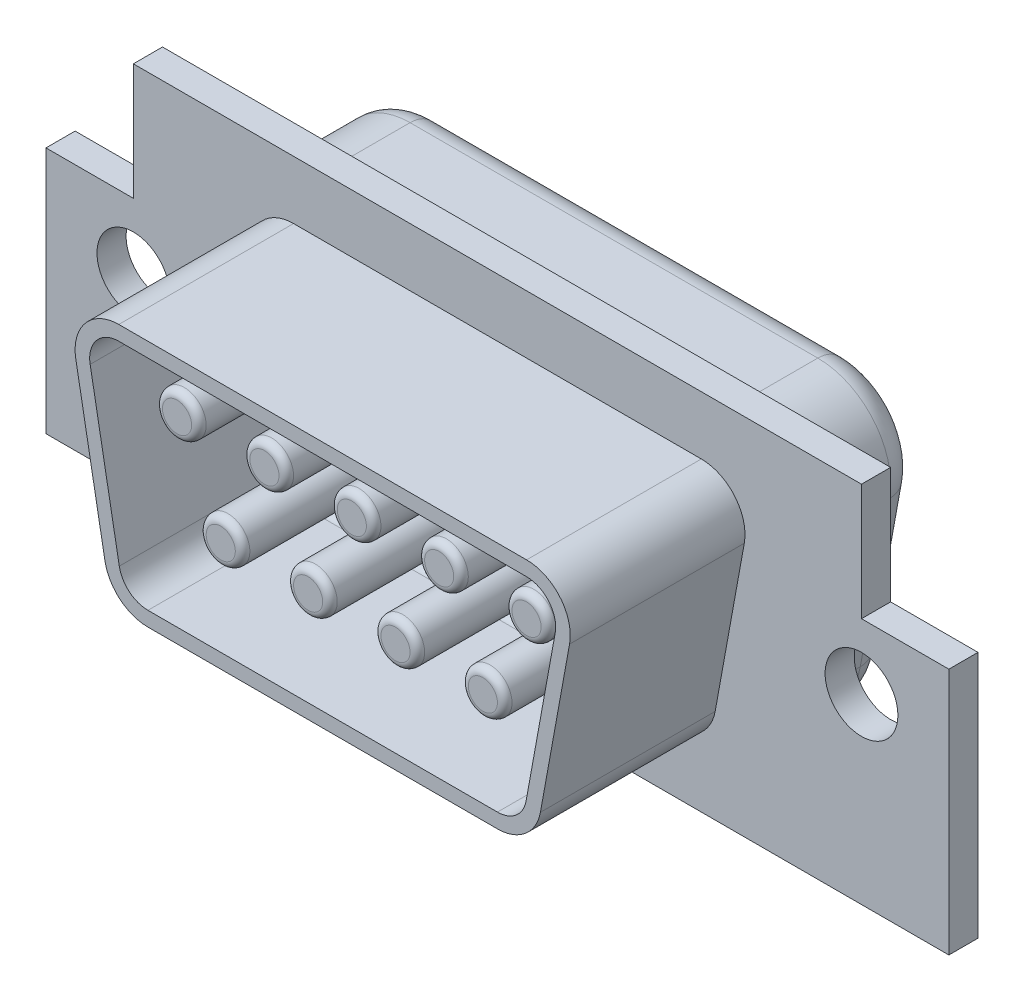
SolidWorks part; units mm, degrees
material "1060 Alloy"
ref_plane "Front Plane" through (0, 0, 0) normal (0, 0, 1) x (1, 0, 0)
ref_plane "Top Plane" through (0, 0, 0) normal (0, 1, 0) x (1, 0, 0)
ref_plane "Right Plane" through (0, 0, 0) normal (1, 0, 0) x (0, 0, -1)
sketch "Sketch1" plane through (0, 0, 0) normal (0, 0, 1) x (1, 0, 0)
  line L0 (-15.5, 6.25) -> (15.5, -6.25) construction
  line L1 (-15.5, 6.25) -> (15.5, 6.25)
  line L2 (-15.5, 6.25) -> (-15.5, -6.25)
  line L3 (-15.5, -6.25) -> (15.5, -6.25)
  line L4 (15.5, 6.25) -> (15.5, -6.25)
  point P4 (0, 0)
  dimension "D1" = 31
  dimension "D2" = 12.5
extrude "Extrude1" add sketch "Sketch1" along normal blind 1
sketch "Sketch2" plane through (0, 0, 1) normal (0, 0, 1) x (1, 0, 0)
  line L5 (7.6692, -4.75) -> (13.0097, -4.8041) construction
  line L6 (-7, 3.75) -> (7, 3.75)
  line L7 (-6, -4.25) -> (6, -4.25)
  line L8 (8.4758, 2.4817) -> (7.4758, -3.0183)
  line L9 (-7, 4.25) -> (7, 4.25)
  line L10 (-8.4758, 2.4817) -> (-7.4758, -3.0183)
  line L11 (7.9839, 2.5711) -> (6.9839, -2.9289)
  line L12 (-6, -3.75) -> (6, -3.75)
  line L13 (-7.9839, 2.5711) -> (-6.9839, -2.9289)
  arc A4 (7.4758, -3.0183) -> (6, -4.25) centre (6, -2.75) cw
  arc A5 (8.4758, 2.4817) -> (7, 4.25) centre (7, 2.75) ccw
  arc A6 (-7, 4.25) -> (-8.4758, 2.4817) centre (-7, 2.75) ccw
  arc A7 (-6, -4.25) -> (-7.4758, -3.0183) centre (-6, -2.75) cw
  arc A8 (7.9839, 2.5711) -> (7, 3.75) centre (7, 2.75) ccw
  arc A9 (6.9839, -2.9289) -> (6, -3.75) centre (6, -2.75) cw
  arc A10 (-6, -3.75) -> (-6.9839, -2.9289) centre (-6, -2.75) cw
  arc A11 (-7, 3.75) -> (-7.9839, 2.5711) centre (-7, 2.75) ccw
  dimension "D8" = 0.5
extrude "Extrude2" add sketch "Sketch2" along normal blind 6
hole_wizard "M3x0.5 Tapped Hole1" positions "3DSketch1" profile "Sketch4" tap size "M3x0.5" standard "Ansi Metric"
sketch3d "3DSketch1"
  line L0 (-15.5, 6.25, 1) -> (-15.5, -6.25, 1) construction
  point P0 (-12.5, 0, 1)
  point P2 (12.5, 0, 1)
  point P7 (-15.5, 0, 1)
  dimension "D1" = 25
  dimension "D2" = 3
sketch "Sketch4" plane through (-12.5, 0, 1) normal (1, 0, 0) x (0, -1, 0)
  line L0 (0, 0) -> (0, 18.2511)
  line L1 (0, 18.2511) -> (1.25, 17.5)
  line L2 (1.25, 17.5) -> (1.25, 0)
  line L5 (1.25, 0) -> (0, 0)
  line L10 (0, 18.2511) -> (-1.25, 17.5) construction
  line L11 (0, -6.35) -> (0, 107.95) construction
  dimension "Tap Drill Dia." = 2.5
  dimension "Tap Drill Depth" = 17.5
  dimension "Drill Angle" = 118
cosmetic thread "Hole Thread1" parameters "D1"=1, "D2"=3
cosmetic thread "Hole Thread2" parameters "D1"=1, "D2"=3
sketch "Sketch6" plane through (0, 0, 0) normal (0, 0, -1) x (-1, 0, 0)
  line L12 (8.4597, -3.1972) -> (9.4597, 2.3028)
  line L13 (-6, -5.25) -> (6, -5.25)
  line L14 (-9.4597, 2.3028) -> (-8.4597, -3.1972)
  line L15 (7, 5.25) -> (-7, 5.25)
  arc A12 (9.4597, 2.3028) -> (7, 5.25) centre (7, 2.75) ccw
  arc A13 (6, -5.25) -> (8.4597, -3.1972) centre (6, -2.75) ccw
  arc A14 (-8.4597, -3.1972) -> (-6, -5.25) centre (-6, -2.75) ccw
  arc A15 (-7, 5.25) -> (-9.4597, 2.3028) centre (-7, 2.75) ccw
extrude "Extrude3" add sketch "Sketch6" along normal blind 4
fillet "Fillet2" radius 1 8 edges at (-8.9597, -0.4472, -4) (-7.6019, -4.6694, -4) (0, -5.25, -4) (7.6019, -4.6694, -4) (8.9597, -0.4472, -4) (8.9194, 4.3519, -4) (0, 5.25, -4) (-8.9194, 4.3519, -4)
sketch "Sketch7" plane through (0, 0, -4) normal (0, 0, -1) x (-1, 0, 0)
  line L12 (6.9839, -2.9289) -> (7.9839, 2.5711)
  line L13 (-6, -3.75) -> (6, -3.75)
  line L14 (-7.9839, 2.5711) -> (-6.9839, -2.9289)
  line L15 (7, 3.75) -> (-7, 3.75)
  arc A12 (7.9839, 2.5711) -> (7, 3.75) centre (7, 2.75) ccw
  arc A13 (6, -3.75) -> (6.9839, -2.9289) centre (6, -2.75) ccw
  arc A14 (-6.9839, -2.9289) -> (-6, -3.75) centre (-6, -2.75) ccw
  arc A15 (-7, 3.75) -> (-7.9839, 2.5711) centre (-7, 2.75) ccw
extrude "Extrude4" add sketch "Sketch7" along normal blind 0.5
sketch "Sketch8" plane through (0, 0, 1) normal (0, 0, 1) x (1, 0, 0)
  line L1 (1.5, -1.5) -> (-1.5, -1.5) construction
  circle A0 centre (-6, 1.5) radius 0.75
  circle A1 centre (-4.5, -1.5) radius 0.75
  circle A2 centre (-3, 1.5) radius 0.75
  circle A3 centre (1.5, -1.5) radius 0.75
  circle A4 centre (0, 1.5) radius 0.75
  circle A5 centre (-1.5, -1.5) radius 0.75
  circle A6 centre (3, 1.5) radius 0.75
  circle A7 centre (4.5, -1.5) radius 0.75
  circle A8 centre (6, 1.5) radius 0.75
  point P19 (0, -1.5)
  dimension "D1" = 1.5
  dimension "D4" = 1.5
  dimension "D5" = 1.5
  dimension "D6" = 1.5
  dimension "D7" = 1.5
  dimension "D8" = 1.5
  dimension "D9" = 1.5
  dimension "D10" = 1.5
  dimension "D11" = 1.5
  dimension "D2" = 3
  dimension "D3" = 1.5
  dimension "D12" = 3
  dimension "D13" = 3
  dimension "D14" = 3
  dimension "D15" = 1.5
  dimension "D16" = 3
  dimension "D17" = 3
  dimension "D18" = 3
sketch "Sketch10" plane through (0, 0, 1) normal (0, 0, 1) x (1, 0, 0)
  line L0 (15.5, 6.25) -> (-15.5, 6.25) construction
  line L1 (-18.9207, 8.4259) -> (-12.5, 8.4259)
  line L2 (-18.9207, 8.4259) -> (-18.9207, 2.25)
  line L3 (-18.9207, 2.25) -> (-12.5, 2.25)
  line L4 (-12.5, 8.4259) -> (-12.5, 2.25)
  line L5 (20.1371, 10.9942) -> (12.5, 10.9942)
  line L6 (20.1371, 10.9942) -> (20.1371, 2.25)
  line L7 (20.1371, 2.25) -> (12.5, 2.25)
  line L8 (12.5, 10.9942) -> (12.5, 2.25)
  line L9 (15.5, -6.25) -> (15.5, 6.25) construction
  line L10 (-15.5, 6.25) -> (-15.5, -6.25) construction
  dimension "D1" = 4
  dimension "D2" = 4
  dimension "D3" = 3
  dimension "D4" = 3
extrude "Cut-Extrude1" cut sketch "Sketch10" against normal blind 5
extrude "Extrude5" add sketch "Sketch8" along normal blind 5
fillet "Fillet3" radius 0.25 26 edges at (6.75, 1.5, 1) (3.75, 1.5, 1) (0.75, 1.5, 1) (-2.25, 1.5, 1) (-5.25, 1.5, 1) (-3.75, -1.5, 1) (2.25, -1.5, 1) (-0.75, -1.5, 1) (5.25, -1.5, 1) (-3.75, -1.5, 6) (-0.75, -1.5, 6) (2.25, -1.5, 6) (5.25, -1.5, 6) (6.75, 1.5, 6) (3.75, 1.5, 6) (0.75, 1.5, 6) (-2.25, 1.5, 6) (-5.25, 1.5, 6) (0, 3.75, 1) (7.7678, 3.3907, 1) (7.4839, -0.1789, 1) (6.6407, -3.5178, 1) (0, -3.75, 1) (-6.6407, -3.5178, 1) (-7.4839, -0.1789, 1) (-7.7678, 3.3907, 1)
